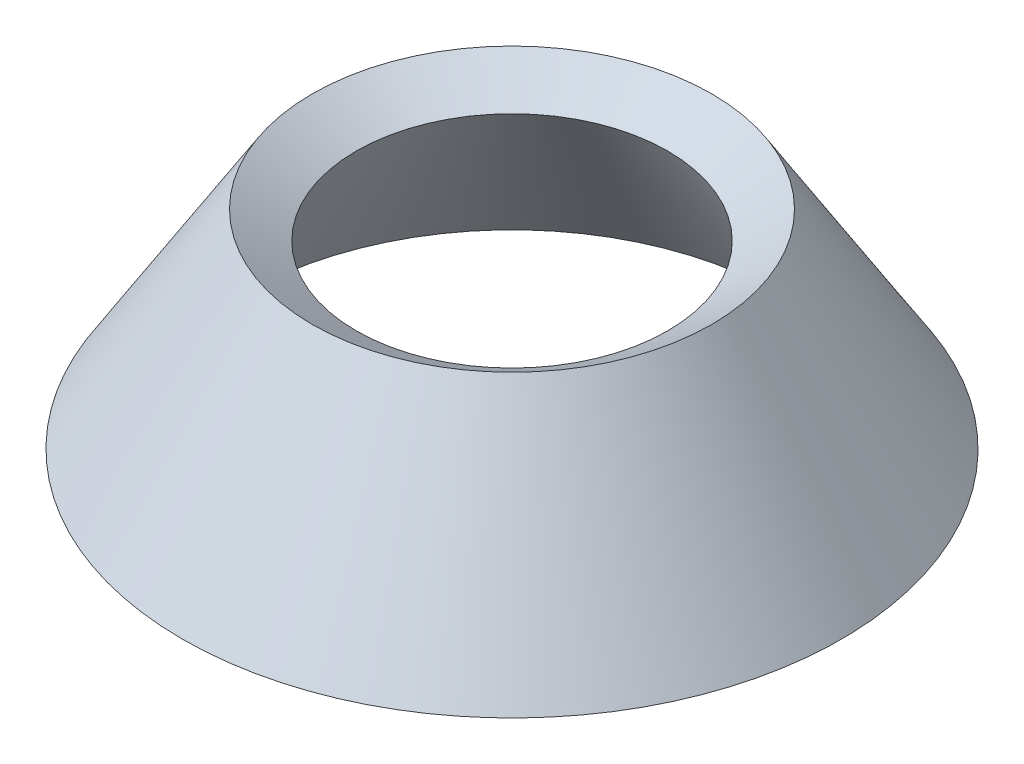
SolidWorks part; units mm, degrees
ref_plane "Plan de face" through (0, 0, 0) normal (0, 0, 1) x (1, 0, 0)
ref_plane "Plan de dessus" through (0, 0, 0) normal (0, 1, 0) x (1, 0, 0)
ref_plane "Plan de droite" through (0, 0, 0) normal (1, 0, 0) x (0, 0, -1)
ref_plane "Plan1" through (0, 0, 40) normal (0, 0, 1) x (1, 0, 0)
sketch "Esquisse1" plane through (0, 0, 0) normal (0, 0, 1) x (1, 0, 0)
  line L0 (0, 0) -> (55, 0) construction
  line L1 (0, 0) -> (0, 40) construction
  line L2 (0, 40) -> (30, 40) construction
  line L3 (55, 0) -> (30, 40)
  dimension "D1" = 30
  dimension "D2" = 55
  dimension "D3" = 40
revolve "Révol.-Mince1" add sketch "Esquisse1" angle 360 about L1
ref_plane "Plan3" through (0, 5.3, 0) normal (0, 1, 0) x (1, 0, 0)
sketch "Esquisse5" plane through (0, 5.3, 0) normal (0, 1, 0) x (1, 0, 0)
  line L1 (-76.7041, 70.9829) -> (74.575, 70.9829)
  line L2 (-76.7041, 70.9829) -> (-76.7041, -71.7171)
  line L3 (-76.7041, -71.7171) -> (74.575, -71.7171)
  line L4 (74.575, 70.9829) -> (74.575, -71.7171)
extrude "Enlèv. mat.-Extru.1" cut sketch "Esquisse5" against normal blind 10
